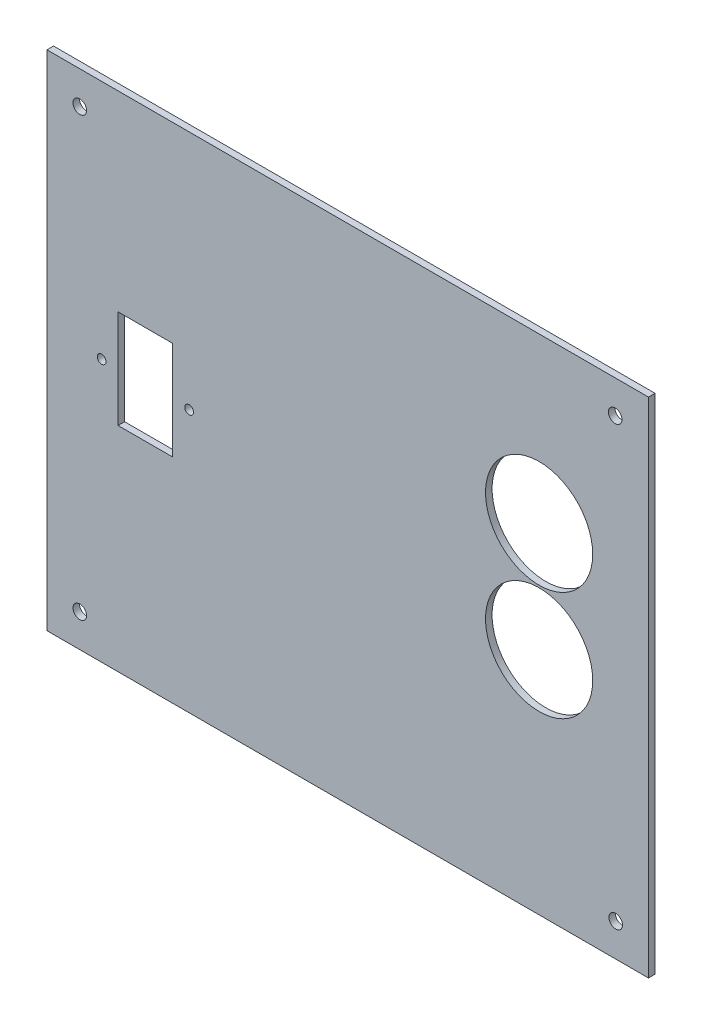
SolidWorks part; units mm, degrees
ref_plane "Alzado" through (0, 0, 0) normal (0, 0, 1) x (1, 0, 0)
ref_plane "Planta" through (0, 0, 0) normal (0, 1, 0) x (1, 0, 0)
ref_plane "Vista lateral" through (0, 0, 0) normal (1, 0, 0) x (0, 0, -1)
sketch "Croquis1" plane through (0, 0, 0) normal (0, 0, 1) x (1, 0, 0)
  line L0 (-122.5, 167.0051) -> (-122.5, -49832.9949) construction
  line L1 (-137.5, 115) -> (137.5, 115)
  line L2 (-137.5, 115) -> (-137.5, -115)
  line L3 (-137.5, -115) -> (137.5, -115)
  line L4 (137.5, 115) -> (137.5, -115)
  line L5 (-137.5, 115) -> (137.5, -115) construction
  line L6 (-137.5, -115) -> (137.5, 115) construction
  line L7 (-173.0544, 100) -> (49826.9456, 100) construction
  line L8 (-226.0645, -100) -> (49773.9355, -100) construction
  line L9 (122.5, 178.733) -> (122.5, -49821.267) construction
  circle A0 centre (-122.5, 100) radius 3.1
  circle A1 centre (122.2752, 100) radius 3.1
  circle A2 centre (-122.5, -100) radius 3.1
  circle A3 centre (122.5, -100) radius 3.1
  point P0 (0, 0)
  dimension "D7" = 6.2
  dimension "D1" = 275
  dimension "D2" = 230
  dimension "D3" = 15
  dimension "D4" = 15
  dimension "D5" = 15
  dimension "D6" = 15
extrude "Saliente-Extruir1" add sketch "Croquis1" along normal blind 3
sketch "Croquis2" plane through (0, 0, 3) normal (0, 0, 1) x (1, 0, 0)
  line L0 (137.5, -115) -> (137.5, 115) construction
  line L2 (62.5, -34.5) -> (112.5, -34.5) construction
  line L3 (62.5, -34.5) -> (62.5, 65.5) construction
  line L4 (62.5, 65.5) -> (112.5, 65.5) construction
  line L5 (112.5, -34.5) -> (112.5, 65.5) construction
  line L6 (62.5, -34.5) -> (112.5, 65.5) construction
  line L7 (62.5, 65.5) -> (112.5, -34.5) construction
  circle A0 centre (87.5, 40) radius 24.5
  circle A1 centre (87.5, -10) radius 24.5
  point P9 (87.5, 15.5)
  dimension "D1" = 49
  dimension "D2" = 50
  dimension "D3" = 10
  dimension "D4" = 50
  dimension "D5" = 50
extrude "Cortar-Extruir1" cut sketch "Croquis2" against normal through all
sketch "Croquis3" plane through (0, 0, 3) normal (0, 0, 1) x (1, 0, 0)
  line L0 (-92.5, 5) -> (49907.5, 5) construction
  line L1 (-105, 27.5) -> (-80, 27.5)
  line L2 (-105, 27.5) -> (-105, -17.5)
  line L3 (-105, -17.5) -> (-80, -17.5)
  line L4 (-80, 27.5) -> (-80, -17.5)
  line L5 (-105, 27.5) -> (-80, -17.5) construction
  line L6 (-105, -17.5) -> (-80, 27.5) construction
  line L7 (-137.5, -115) -> (137.5, -115) construction
  line L8 (137.5, -115) -> (137.5, 115) construction
  circle A0 centre (-112.5, 5) radius 2
  circle A1 centre (-72.5, 5) radius 2
  point P4 (-92.5, 5)
  dimension "D1" = 4
  dimension "D2" = 20
  dimension "D3" = 20
  dimension "D4" = 45
  dimension "D5" = 25
  dimension "D6" = 120
  dimension "D7" = 230
extrude "Cortar-Extruir2" cut sketch "Croquis3" against normal through all
